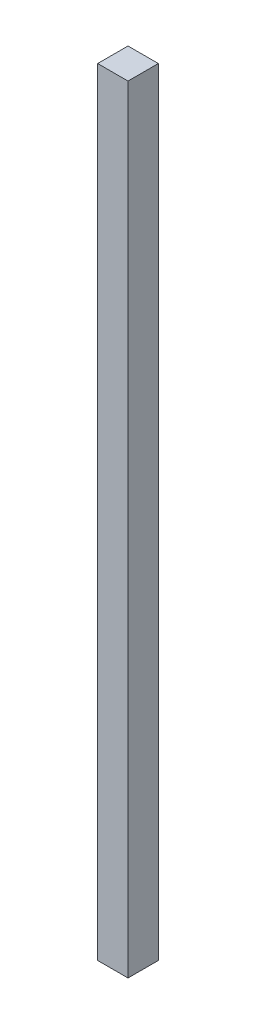
SolidWorks part; units mm, degrees
ref_plane "Спереди" through (0, 0, 0) normal (0, 0, 1) x (1, 0, 0)
ref_plane "Сверху" through (0, 0, 0) normal (0, 1, 0) x (1, 0, 0)
ref_plane "Справа" through (0, 0, 0) normal (1, 0, 0) x (0, 0, -1)
sketch "Эскиз1" plane through (0, 0, 0) normal (0, 1, 0) x (1, 0, 0)
  line L1 (5, -5) -> (-5, -5)
  line L2 (5, -5) -> (5, 5)
  line L3 (5, 5) -> (-5, 5)
  line L4 (-5, -5) -> (-5, 5)
  line L5 (5, -5) -> (-5, 5) construction
  line L6 (5, 5) -> (-5, -5) construction
  point P0 (0, 0)
  dimension "D1" = 10
extrude "Бобышка-Вытянуть1" add sketch "Эскиз1" along normal blind 256
